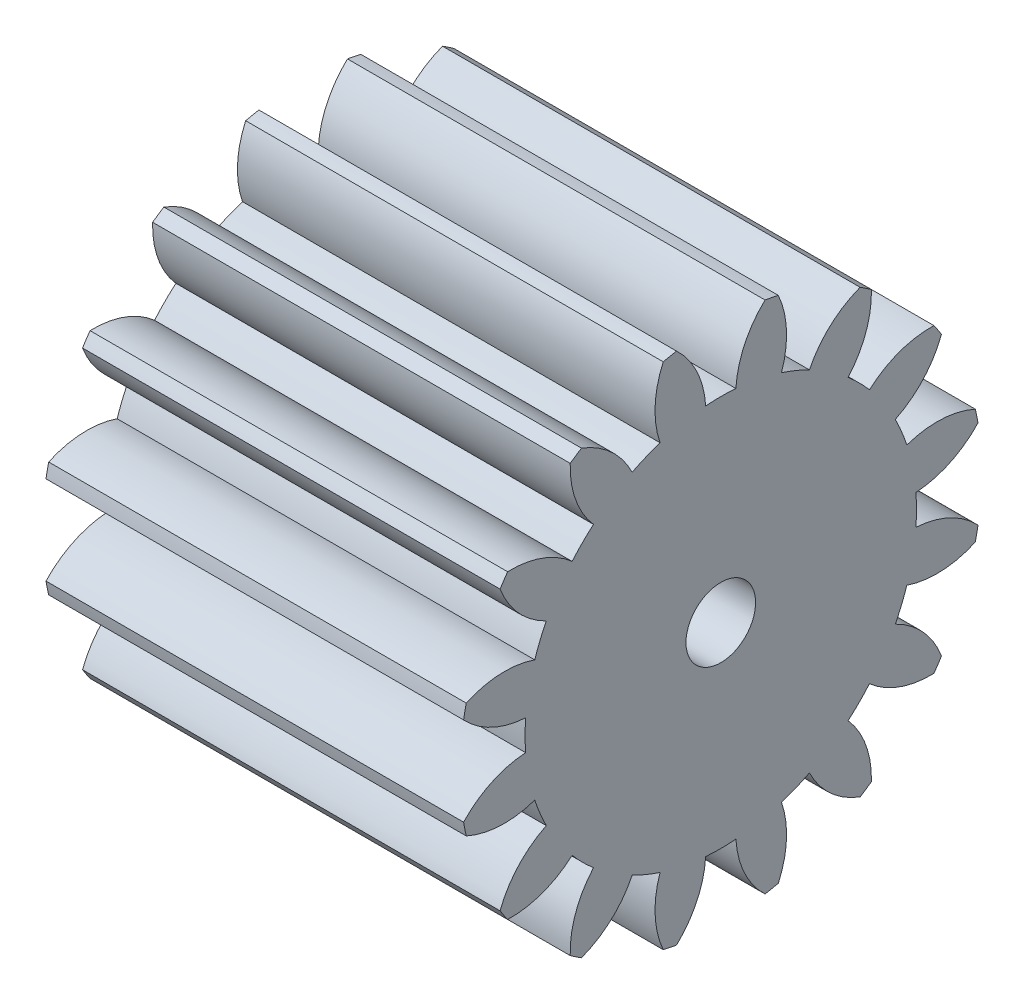
SolidWorks part; units mm, degrees
ref_plane "Plane1" through (0, 0, 0) normal (0, 0, 1) x (1, 0, 0)
ref_plane "Plane2" through (0, 0, 0) normal (0, 1, 0) x (1, 0, 0)
ref_plane "Plane3" through (0, 0, 0) normal (1, 0, 0) x (0, 0, -1)
other "Configuration Table"
sketch "HoldingSke" plane through (0, 0, 0) normal (0, 1, 0) x (1, 0, 0)
  line L0 (0, 0) -> (0.769, -0.2205)
  line L1 (-15, 0) -> (100, 0) construction
  line L2 (0, 0) -> (-2.1039, 2.3779)
  line L3 (0, 0) -> (-11.863, 4.5341)
  line L4 (0, 0) -> (8.3015, 2.3804)
  line L5 (0, 0) -> (-46.8476, -17.4728)
  line L6 (0, 0) -> (-14.9213, -10.0675)
  line L7 (-2.1039, 2.3779) -> (8.6586, 51.2059)
  line L8 (-76.2, 54.61) -> (-75.7, 54.61)
  line L9 (-71.009, 38.7566) -> (-53.1078, 45.2721)
  line L10 (-76.2, 71.12) -> (104.1128, 71.12)
  line L11 (0, 0) -> (-18, 0)
  line L12 (-76.2, 101.6) -> (-76.155, 101.6)
  line L13 (24.9733, 27.94) -> (52.9518, 28.4284)
  line L14 (24.9733, 27.94) -> (24.9743, 27.94)
  line L15 (24.9733, 27.94) -> (100.4006, 29.5858)
  line L16 (-63.627, -1.25) -> (-12.827, -1.25)
  circle A0 centre (0, 0) radius 1.5
  circle A1 centre (0, 0) radius 8.4365
  circle A2 centre (0, 0) radius 37.5
  circle A3 centre (0, 0) radius 1.5
  dimension "Hub_dia" = 75
  dimension "Bore" = 3
  dimension "MBD" = 3
  dimension "Overall_len" = 50
  dimension "OAL" = 50.0001
  dimension "T_dim" = 0.5
  dimension "H" = 19.05
  dimension "Pitch_radius" = 180.3128
  dimension "Addendum_fac" = 1
  dimension "Dedendum_fac" = 1.25
  dimension "Clearance_fac" = 0.25
  dimension "Dedendum_add" = 0.001
sketch "BasProSke" plane through (0, 0, 0) normal (0, 1, 0) x (1, 0, 0)
  line L0 (-10, 0) -> (60, 0) construction
  line L1 (0, 0) -> (0, 11.25)
  line L2 (0, 0) -> (18, 0)
  line L3 (18, 0) -> (18, 11.25)
  line L4 (18, 11.25) -> (0, 11.25)
revolve "Base-Revolve" add sketch "BasProSke" angle 360 about L0
sketch "TooCutSke" plane through (0, 0, 0) normal (1, 0, 0) x (0, 0, -1)
  line L1 (0, 0) -> (0, 107) construction
  line L2 (0, 0) -> (-1.0589, 9.9438) construction
  line L3 (0, 0) -> (-3.8859, 19.5358) construction
  line L4 (-1.0589, 9.9438) -> (-1.943, 9.7679) construction
  arc A0 (0.6511, 8.4113) -> (-0.6511, 8.4113) centre (0, 0) ccw
  arc A1 (1.9309, 11.1088) -> (-1.9309, 11.1088) centre (0, 0) ccw
  circle A2 centre (0, 0) radius 10 construction
  circle A3 centre (0, 0) radius 9.3969 construction
  arc A4 (-0.6511, 8.4113) -> (-1.9309, 11.1088) centre (-4.6437, 8.1693) ccw
  arc A5 (1.9309, 11.1088) -> (0.6511, 8.4113) centre (4.6437, 8.1693) ccw
extrude "ToothCut" cut sketch "TooCutSke" along normal through all
fillet "Breaks" [suppressed] radius 0.025
fillet "RootFillets" [suppressed] radius 0.3135
pattern_circular "TeethCuts" count 16 every 22.5 about axis through (-10, 0, 0) along (1, 0, 0) of "ToothCut", "RootFillets", "Breaks"
sketch "HubNeaOneSke" plane through (0, 0, 0) normal (-1, 0, 0) x (0, 0, 1)
  circle A0 centre (0, 0) radius 8.4365
extrude "HubNearOne" [suppressed] add sketch "HubNeaOneSke" along normal blind 32.0001
sketch "HubNeaBotSke" plane through (0, 0, 0) normal (-1, 0, 0) x (0, 0, 1)
  circle A0 centre (0, 0) radius 8.4365
extrude "HubNearBoth" [suppressed] add sketch "HubNeaBotSke" along normal blind 16
ref_plane "FarPln" through (18, 0, 0) normal (1, 0, 0) x (0, 0, -1)
sketch "HubFarSke" plane through (18, 0, 0) normal (1, 0, 0) x (0, 0, -1)
  circle A0 centre (0, 0) radius 8.4365
extrude "HubFar" [suppressed] add sketch "HubFarSke" along normal blind 16
sketch "BorSke" plane through (0, 0, 0) normal (1, 0, 0) x (0, 0, -1)
  circle A0 centre (0, 0) radius 1.5
  dimension "Diameter" = 3
extrude "Bore" cut sketch "BorSke" along normal mid plane 100.0001
sketch "KeySke" plane through (0, 0, 0) normal (1, 0, 0) x (0, 0, -1)
  line L0 (-0.6, 0) -> (-0.6, 2)
  line L1 (-0.6, 2) -> (0.6, 2)
  line L2 (0.6, 2) -> (0.6, 0)
  line L3 (0, 0) -> (0, 34) construction
  line L4 (-0.6, 0) -> (0.6, 0)
  dimension "Offset" = 2
  dimension "Width" = 1.2
extrude "Keyway" [suppressed] cut sketch "KeySke" along normal mid plane 100.0001
pattern_circular "Keyway2" [suppressed] count 2 every 90 about axis through (-10, 0, 0) along (1, 0, 0)
equation "' \"Module@HoldingSke\" = 6.35"
equation "' \"Num_teeth@HoldingSke\" = 12"
equation "' \"Ap@HoldingSke\" =  20"
equation "' \"Ap@HoldingSke\" = 20"
equation "' \"Width@HoldingSke\" = 0.5 * 25.4"
equation "' \"Hub_dia@HoldingSke\"= 1 * 25.4"
equation "' \"Hub_dia@HoldingSke\" = 1 * 25.4"
equation "' \"Overall_len@HoldingSke\" = 1.0 * 25.4"
equation "' \"Bore@HoldingSke\" = 0.75 * 25.4"
equation "' \"T_dim@HoldingSke\" = 0.1 * 25.4"
equation "' \"Width@KeySke\" = 0.25 * 25.4"
equation "' \"Show_teeth@HoldingSke\" = 13"
equation "' \"Backlash@HoldingSke\" = 0.009 * 25.4"
equation "' \"Addendum_fac@HoldingSke\" = 1.0"
equation "' \"Dedendum_fac@HoldingSke\" = 1.25"
equation "' \"Dedendum_add@HoldingSke\" = 0.00005 * 25.4"
equation "' \"Clearance_fac@HoldingSke\" = 0.25"
equation "\"Pitch@HoldingSke\" = 1 / \"Module@HoldingSke\""
equation "\"Overcut_dia@TooCutSke\" = (\"Num_teeth@HoldingSke\" + 2 * \"Addendum_fac@HoldingSke\") / \"Pitch@HoldingSke\" + 0.002 * 25.4"
equation "\"Pitch_dia@TooCutSke\" = \"Num_teeth@HoldingSke\" / \"Pitch@HoldingSke\""
equation "\"Base_dia@TooCutSke\" = \"Num_teeth@HoldingSke\" / \"Pitch@HoldingSke\" * cos((\"Ap@HoldingSke\"  * 3.14159265 / 180))"
equation "\"Root_dia@TooCutSke\" = (\"Num_teeth@HoldingSke\" + 2) / \"Pitch@HoldingSke\" - 2 * (\"Addendum_fac@HoldingSke\" + \"Dedendum_fac@HoldingSke\") / \"Pitch@HoldingSke\" - \"Dedendum_add@HoldingSke\" * 2"
equation "\"Half_ang@TooCutSke\" = 180 / \"Num_teeth@HoldingSke\""
equation "\"Half_CT@TooCutSke\" = \"Num_teeth@HoldingSke\" / \"Pitch@HoldingSke\" * sin((3.14159265 / 2 / \"Num_teeth@HoldingSke\")) / 2 - 7 * \"Backlash@HoldingSke\" / 4"
equation "\"Flank_rad@TooCutSke\" = \"Num_teeth@HoldingSke\" / \"Pitch@HoldingSke\" / 5"
equation "\"Radius@RootFillets\" = \"Clearance_fac@HoldingSke\" / \"Pitch@HoldingSke\" + \"Dedendum_add@HoldingSke\""
equation "\"Break_rad@Breaks\" = 0.02 / \"Pitch@HoldingSke\""
equation "\"Thickness@HoldingSke\" = \"Width@HoldingSke\""
equation "\"OAL@HoldingSke\" = \"Thickness@HoldingSke\""
equation "\"MHD@HoldingSke\" = (\"Num_teeth@HoldingSke\" + 2) / \"Pitch@HoldingSke\" - 2 * (\"Addendum_fac@HoldingSke\" + \"Dedendum_fac@HoldingSke\")  / \"Pitch@HoldingSke\" - \"Dedendum_add@HoldingSke\" * 2"
equation "\"MBD@HoldingSke\" = (\"Num_teeth@HoldingSke\" + 2) / \"Pitch@HoldingSke\" - 2 * (\"Addendum_fac@HoldingSke\" + \"Dedendum_fac@HoldingSke\")  / \"Pitch@HoldingSke\" - \"Dedendum_add@HoldingSke\" * 2 - 0.002 * 25.4"
equation "\"MHD@HoldingSke\" = ((sgn( \"MHD@HoldingSke\" - \"Hub_dia@HoldingSke\" )-1)*( \"MHD@HoldingSke\" - \"Hub_dia@HoldingSke\" ))/-2+ \"Hub_dia@HoldingSke\""
equation "\"MBD@HoldingSke\" = ((sgn( \"MBD@HoldingSke\" - \"Bore@HoldingSke\" )-1)*( \"MBD@HoldingSke\" - \"Bore@HoldingSke\" ))/-2+ \"Bore@HoldingSke\""
equation "\"OAL@HoldingSke\" = ((sgn( \"OAL@HoldingSke\" - \"Overall_len@HoldingSke\" )+1)*( \"OAL@HoldingSke\" - \"Overall_len@HoldingSke\" ))/2 + \"Overall_len@HoldingSke\" + 0.000002 * 25.4"
equation "\"Num_teeth@TeethCuts\" = int( \"Show_teeth@HoldingSke\" ) + 1"
equation "\"Num_teeth@TeethCuts\" = ((sgn( \"Num_teeth@TeethCuts\" - \"Num_teeth@HoldingSke\" )-1)*( \"Num_teeth@TeethCuts\" - \"Num_teeth@HoldingSke\" ))/-2+ \"Num_teeth@HoldingSke\""
equation "\"Num_teeth@TeethCuts\" = ((sgn( \"Num_teeth@TeethCuts\" - 2.0)+1)*( \"Num_teeth@TeethCuts\" - 2.0))/2 +2.0"
equation "\"Angle@TeethCuts\" = 360.0 / \"Num_teeth@HoldingSke\""
equation "\"Diameter@BasProSke\" = (\"Num_teeth@HoldingSke\" + 2 * \"Addendum_fac@HoldingSke\") / \"Pitch@HoldingSke\""
equation "\"Thickness@BasProSke\"  = \"Thickness@HoldingSke\""
equation "' \"Fillet_rad@BasProSke\" =  \"Thickness@HoldingSke\" * 0.05"
equation "' \"Fillet_rad@BasProSke\" = \"Thickness@HoldingSke\" * 0.05"
equation "\"MHD@HoldingSke\" = ((sgn( \"MHD@HoldingSke\" - \"Root_dia@TooCutSke\" )-1)*( \"MHD@HoldingSke\" - \"Root_dia@TooCutSke\" ))/-2+ \"Root_dia@TooCutSke\""
equation "\"Diameter@HubNeaOneSke\" = \"MHD@HoldingSke\""
equation "\"Length@HubNearOne\" = \"OAL@HoldingSke\" - \"Thickness@BasProSke\""
equation "\"Diameter@HubNeaBotSke\" = \"MHD@HoldingSke\""
equation "\"Length@HubNearBoth\" = ( \"OAL@HoldingSke\" - \"Thickness@BasProSke\" ) / 2.0"
equation "\"Thickness@FarPln\" = \"Thickness@BasProSke\""
equation "\"Diameter@HubFarSke\" = \"MHD@HoldingSke\""
equation "\"Length@HubFar\" = ( \"OAL@HoldingSke\" - \"Thickness@BasProSke\" ) / 2.0"
equation "\"Diameter@BorSke\" = \"MBD@HoldingSke\""
equation "\"D1@Bore\" = \"OAL@HoldingSke\" * 2.0"
equation "\"D1@Keyway\" = \"OAL@HoldingSke\" * 2.0"
equation "\"Offset@KeySke\" = \"T_dim@HoldingSke\" + \"MBD@HoldingSke\" / 2.0"
